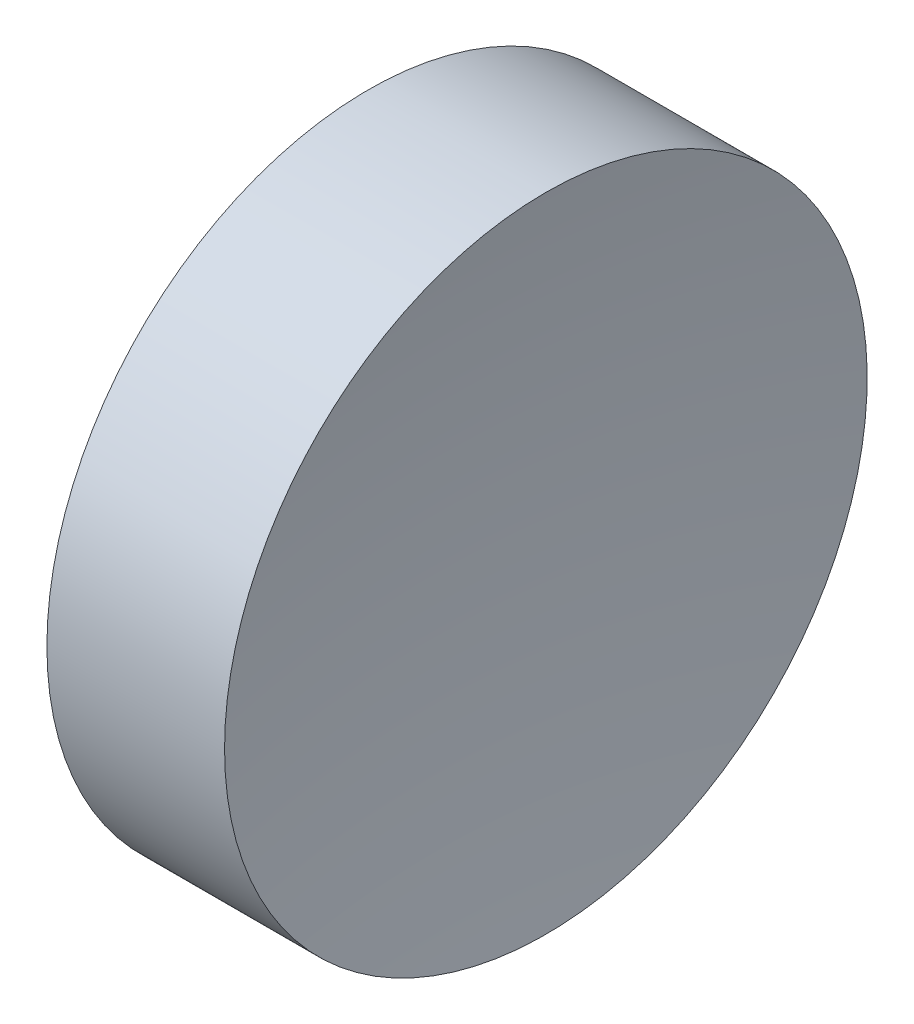
SolidWorks part; units mm, degrees
ref_plane "前视基准面" through (0, 0, 0) normal (0, 0, 1) x (1, 0, 0)
ref_plane "上视基准面" through (0, 0, 0) normal (0, 1, 0) x (1, 0, 0)
ref_plane "右视基准面" through (0, 0, 0) normal (1, 0, 0) x (0, 0, -1)
sketch "草图1" plane through (0, 0, 0) normal (0, 0, 1) x (1, 0, 0)
  line L0 (20.684, 13.0311) -> (26.997, 13.0311) construction
  line L1 (22.3093, 13.0311) -> (22.3093, 16.1811)
  line L2 (22.3093, 16.1811) -> (24.0509, 16.1811)
  line L3 (23.8093, 13.0311) -> (22.3093, 13.0311)
  arc A0 (24.0509, 16.1811) -> (23.8093, 13.0311) centre (44.4593, 13.0311) ccw
revolve "旋转1" add sketch "草图1" angle 360 about L0
